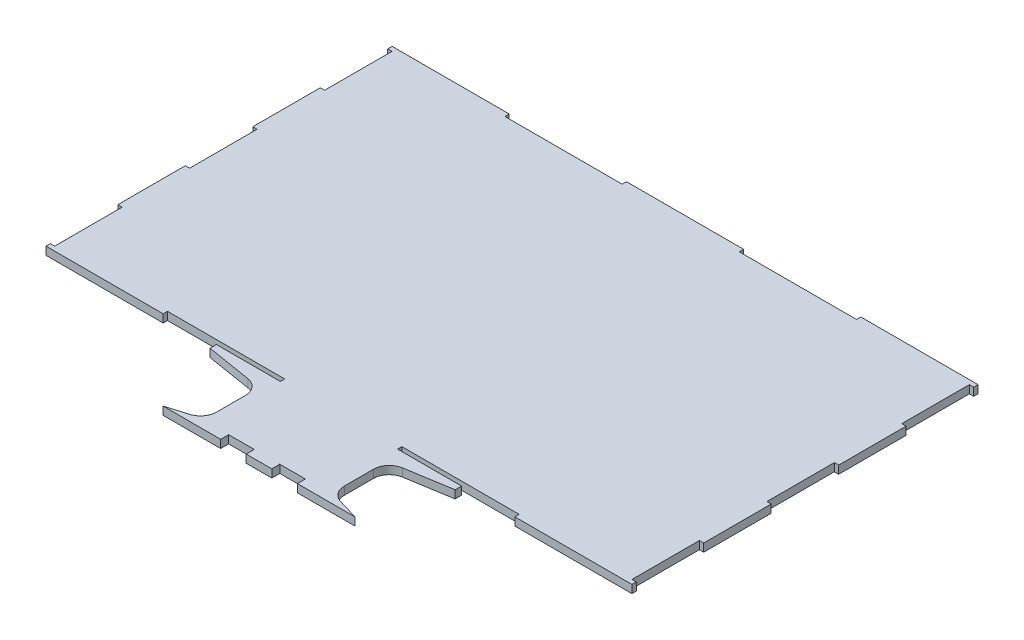
SolidWorks part; units mm, degrees
ref_plane "Front Plane" through (0, 0, 0) normal (0, 0, 1) x (1, 0, 0)
ref_plane "Top Plane" through (0, 0, 0) normal (0, 1, 0) x (1, 0, 0)
ref_plane "Right Plane" through (0, 0, 0) normal (1, 0, 0) x (0, 0, -1)
sketch "Sketch1" plane through (0, 0, 0) normal (0, 1, 0) x (1, 0, 0)
  line L0 (-183.2, 108.2) -> (-109.92, 108.2)
  line L1 (-109.92, 105.5) -> (-36.64, 105.5)
  line L4 (180.5, 105.5) -> (180.5, 63.3)
  line L5 (183.2, 108.2) -> (183.2, 105.5)
  line L8 (183.2, 63.3) -> (183.2, 21.1)
  line L9 (183.2, 108.2) -> (183.2, -108.2) construction
  line L10 (180.5, -105.5) -> (183.2, -105.5)
  line L11 (180.5, 105.5) -> (183.2, 105.5)
  line L13 (180.5, 105.5) -> (180.5, -105.5) construction
  line L14 (180.5, 21.1) -> (180.5, -21.1)
  line L16 (180.5, -63.3) -> (180.5, -105.5)
  line L18 (-180.5, 105.5) -> (-180.5, -105.5) construction
  line L23 (-183.2, 108.2) -> (183.2, 108.2) construction
  line L24 (-36.64, 108.2) -> (36.64, 108.2)
  line L26 (109.92, 108.2) -> (183.2, 108.2)
  line L27 (-109.92, 108.2) -> (-109.92, 105.5)
  line L28 (-36.64, 108.2) -> (-36.64, 105.5)
  line L29 (36.64, 108.2) -> (36.64, 105.5)
  line L30 (109.92, 108.2) -> (109.92, 105.5)
  line L31 (-180.5, 105.5) -> (180.5, 105.5) construction
  line L32 (36.64, 105.5) -> (109.92, 105.5)
  line L33 (-183.2, -108.2) -> (183.2, -108.2) construction
  line L34 (-180.5, -105.5) -> (180.5, -105.5) construction
  line L35 (180.5, -21.1) -> (183.2, -21.1)
  line L36 (109.92, -108.2) -> (183.2, -108.2)
  line L37 (109.92, -108.2) -> (109.92, -105.5)
  line L38 (36.64, -105.5) -> (109.92, -105.5)
  line L39 (36.64, -108.2) -> (36.64, -105.5)
  line L41 (-36.64, -108.2) -> (-36.64, -105.5)
  line L42 (-109.92, -105.5) -> (-36.64, -105.5)
  line L43 (-109.92, -108.2) -> (-109.92, -105.5)
  line L44 (-183.2, -108.2) -> (-109.92, -108.2)
  line L45 (180.5, -63.3) -> (183.2, -63.3)
  line L46 (180.5, 21.1) -> (183.2, 21.1)
  line L47 (180.5, 63.3) -> (183.2, 63.3)
  line L48 (183.2, -21.1) -> (183.2, -63.3)
  line L49 (-183.2, 108.2) -> (-183.2, -108.2) construction
  line L50 (183.2, -105.5) -> (183.2, -108.2)
  line L51 (-40, -126.6956) -> (-40, -144.7597)
  line L52 (-183.2, -105.5) -> (-183.2, -108.2)
  line L53 (-180.5, -105.5) -> (-183.2, -105.5)
  line L54 (-180.5, -63.3) -> (-180.5, -105.5)
  line L55 (-180.5, -63.3) -> (-183.2, -63.3)
  line L56 (-183.2, -21.1) -> (-183.2, -63.3)
  line L57 (-180.5, -21.1) -> (-183.2, -21.1)
  line L58 (-180.5, 21.1) -> (-180.5, -21.1)
  line L59 (-180.5, 21.1) -> (-183.2, 21.1)
  line L60 (-183.2, 63.3) -> (-183.2, 21.1)
  line L61 (-180.5, 63.3) -> (-183.2, 63.3)
  line L62 (-180.5, 105.5) -> (-180.5, 63.3)
  line L63 (-183.2, 108.2) -> (-183.2, 105.5)
  line L64 (-180.5, 105.5) -> (-183.2, 105.5)
  line L67 (40, -126.6956) -> (40, -144.7597)
  line L70 (-40, -158.2) -> (-24, -158.2)
  line L71 (24, -153.2) -> (8, -153.2)
  line L75 (-8, -158.2) -> (8, -158.2)
  line L77 (24, -158.2) -> (40, -158.2)
  line L78 (-24, -158.2) -> (-24, -153.2)
  line L79 (-8, -158.2) -> (-8, -153.2)
  line L80 (8, -158.2) -> (8, -153.2)
  line L81 (24, -158.2) -> (24, -153.2)
  line L82 (-8, -153.2) -> (-24, -153.2)
  line L83 (-36.64, -108.2) -> (-76.64, -108.2)
  line L84 (36.64, -108.2) -> (76.64, -108.2)
  line L85 (-76.64, -108.2) -> (-76.64, -112.2)
  line L86 (-76.64, -112.2) -> (-48.384, -116.8271)
  line L87 (76.64, -108.2) -> (76.64, -112.2)
  line L88 (76.64, -112.2) -> (48.384, -116.8271)
  line L89 (-40, -158.2) -> (-60, -158.2)
  line L90 (40, -158.2) -> (60, -158.2)
  line L92 (-47.1265, -154.338) -> (-60, -158.2)
  line L94 (47.1265, -154.338) -> (60, -158.2)
  arc A0 (-48.384, -116.8271) -> (-40, -126.6956) centre (-50, -126.6956) cw
  arc A1 (40, -126.6956) -> (48.384, -116.8271) centre (50, -126.6956) cw
  arc A2 (-47.1265, -154.338) -> (-40, -144.7597) centre (-50, -144.7597) ccw
  arc A3 (40, -144.7597) -> (47.1265, -154.338) centre (50, -144.7597) ccw
  point P0 (0, 0)
  point P58 (-40, -118.2)
  point P68 (40, -118.2)
  dimension "D2" = 10
  dimension "D3" = 10
  dimension "D6" = 10
  dimension "D7" = 10
  dimension "D1" = 2.7
  dimension "D4" = 40
  dimension "D5" = 40
extrude "Boss-Extrude1" add sketch "Sketch1" along normal blind 5
